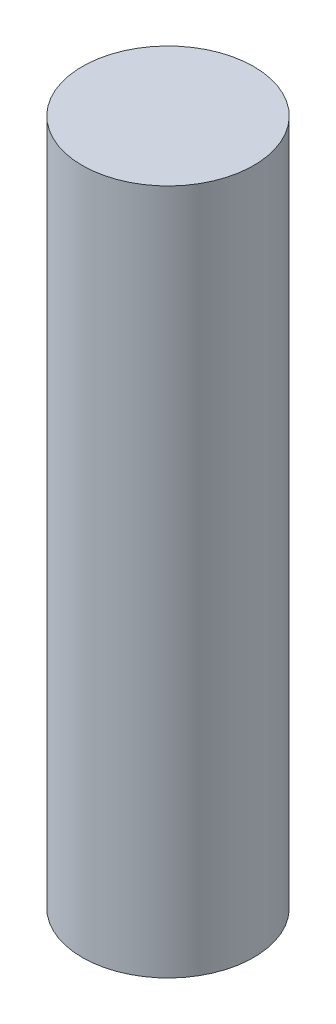
SolidWorks part; units mm, degrees
ref_plane "Front Plane" through (0, 0, 0) normal (0, 0, 1) x (1, 0, 0)
ref_plane "Top Plane" through (0, 0, 0) normal (0, 1, 0) x (1, 0, 0)
ref_plane "Right Plane" through (0, 0, 0) normal (1, 0, 0) x (0, 0, -1)
sketch "Sketch1" plane through (0, 0, 0) normal (0, 1, 0) x (1, 0, 0)
  circle A0 centre (0, 0) radius 3.175
  dimension "D1" = 6.35
extrude "Boss-Extrude1" add sketch "Sketch1" along normal blind 25.4
